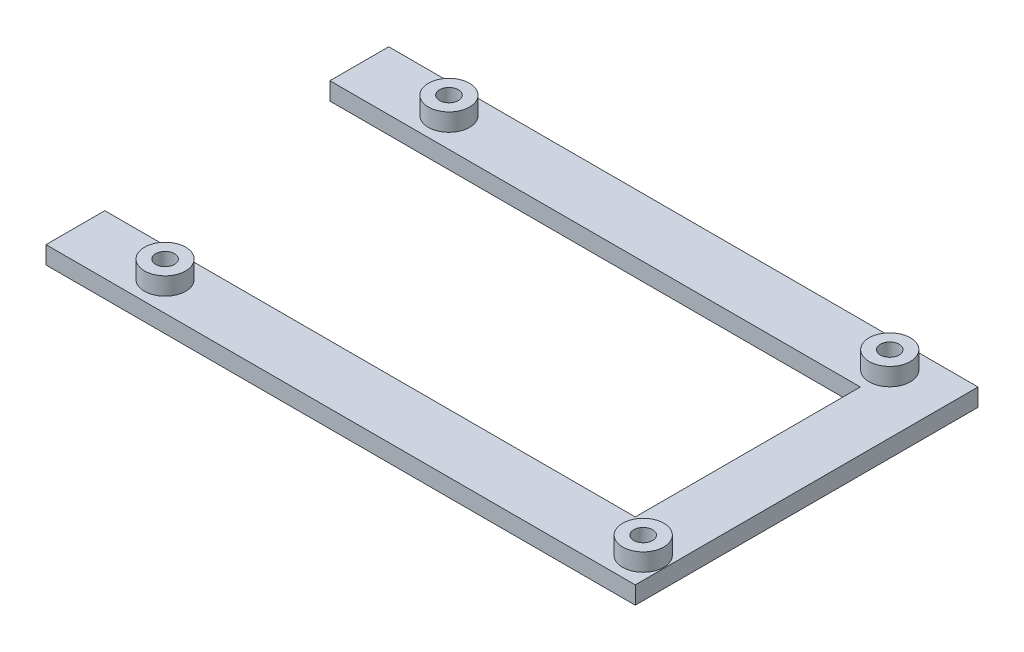
SolidWorks part; units mm, degrees
ref_plane "Front Plane" through (0, 0, 0) normal (0, 0, 1) x (1, 0, 0)
ref_plane "Top Plane" through (0, 0, 0) normal (0, 1, 0) x (1, 0, 0)
ref_plane "Right Plane" through (0, 0, 0) normal (1, 0, 0) x (0, 0, -1)
sketch "Sketch1" plane through (0, 0, 0) normal (0, 1, 0) x (1, 0, 0)
  line L1 (0, 7.54) -> (90.17, 7.54)
  line L2 (0, 7.54) -> (0, -2.46)
  line L3 (0, -2.46) -> (100.17, -2.46)
  line L5 (0, 45.8) -> (90.17, 45.8)
  line L6 (0, 45.8) -> (0, 55.8)
  line L9 (90.17, 7.54) -> (90.17, 45.8)
  line L10 (0, 55.8) -> (100.17, 55.8)
  line L11 (100.17, -2.46) -> (100.17, 55.8)
  circle A0 centre (15.24, 2.54) radius 1.6
  circle A1 centre (96.52, 2.54) radius 1.6
  circle A2 centre (15.24, 50.8) radius 1.6
  circle A3 centre (90.17, 50.8) radius 1.6
  dimension "D1" = 15.24
  dimension "D2" = 2.54
  dimension "D3" = 3.2
  dimension "D4" = 2.54
  dimension "D6" = 48.26
  dimension "D8" = 74.93
  dimension "D9" = 48.26
  dimension "D12" = 5
  dimension "D5" = 96.52
  dimension "D7" = 15.24
  dimension "D10" = 10
  dimension "D11" = 5
  dimension "D13" = 10
  dimension "D15" = 10
extrude "Boss-Extrude1" add sketch "Sketch1" along normal blind 3 contours L5 L9 L1 L2 L3 L11 L10 L6 | A0 | A2 | A1 | A3
sketch "Sketch2" plane through (0, 3, 0) normal (0, 1, 0) x (1, 0, 0)
  circle A0 centre (15.24, 50.8) radius 3.5
  circle A1 centre (90.17, 50.8) radius 3.5
  circle A2 centre (96.52, 2.54) radius 3.5
  circle A3 centre (15.24, 2.54) radius 3.5
  circle A4 centre (15.24, 50.8) radius 1.6
  circle A5 centre (90.17, 50.8) radius 1.6
  circle A6 centre (96.52, 2.54) radius 1.6
  circle A7 centre (15.24, 2.54) radius 1.6
  dimension "D1" = 7
extrude "Boss-Extrude2" add sketch "Sketch2" along normal blind 3
